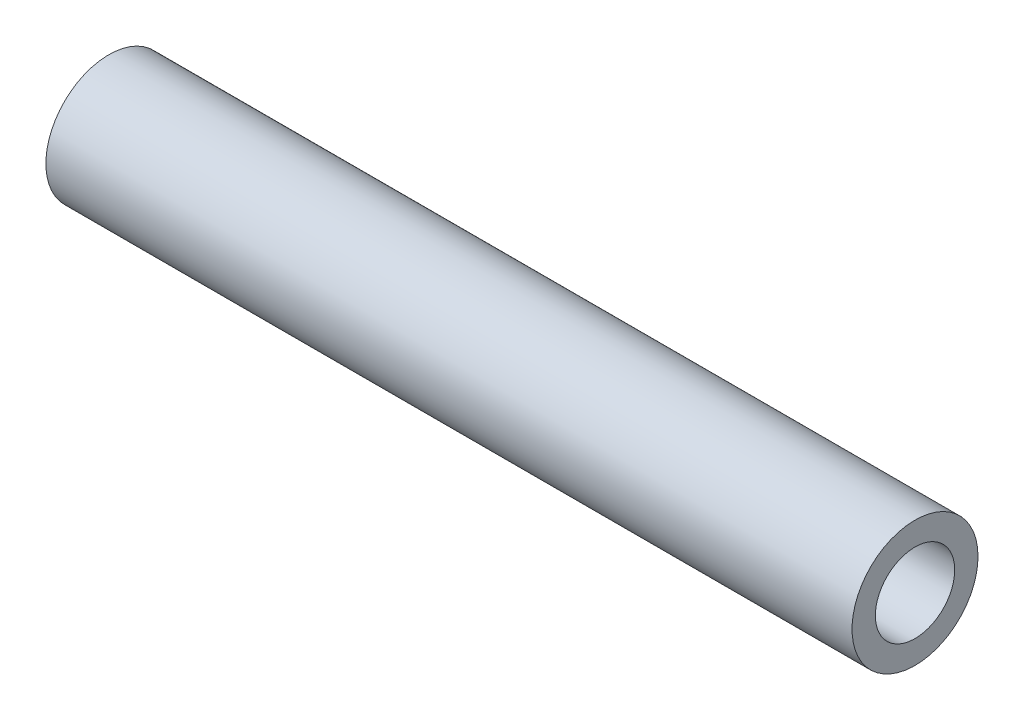
SolidWorks part; units mm, degrees
material "6061-T6 (SS)"
ref_plane "Front Plane" through (0, 0, 0) normal (0, 0, 1) x (1, 0, 0)
ref_plane "Top Plane" through (0, 0, 0) normal (0, 1, 0) x (1, 0, 0)
ref_plane "Right Plane" through (0, 0, 0) normal (1, 0, 0) x (0, 0, -1)
sketch "Sketch1" plane through (0, 0, 0) normal (1, 0, 0) x (0, 0, -1)
  circle A0 centre (0, 0) radius 3.9688
  dimension "D1" = 7.9375
extrude "Boss-Extrude1" add sketch "Sketch1" along normal mid plane 50.8
sketch "Sketch2" plane through (25.4, 0, 0) normal (1, 0, 0) x (0, 0, -1)
  circle A0 centre (0, 0) radius 2.5
  dimension "D1" = 5
extrude "Cut-Extrude1" cut sketch "Sketch2" against normal blind 12.7
mirror "Mirror1" about plane through (0, 0, 0) normal (1, 0, 0) of "Cut-Extrude1"
